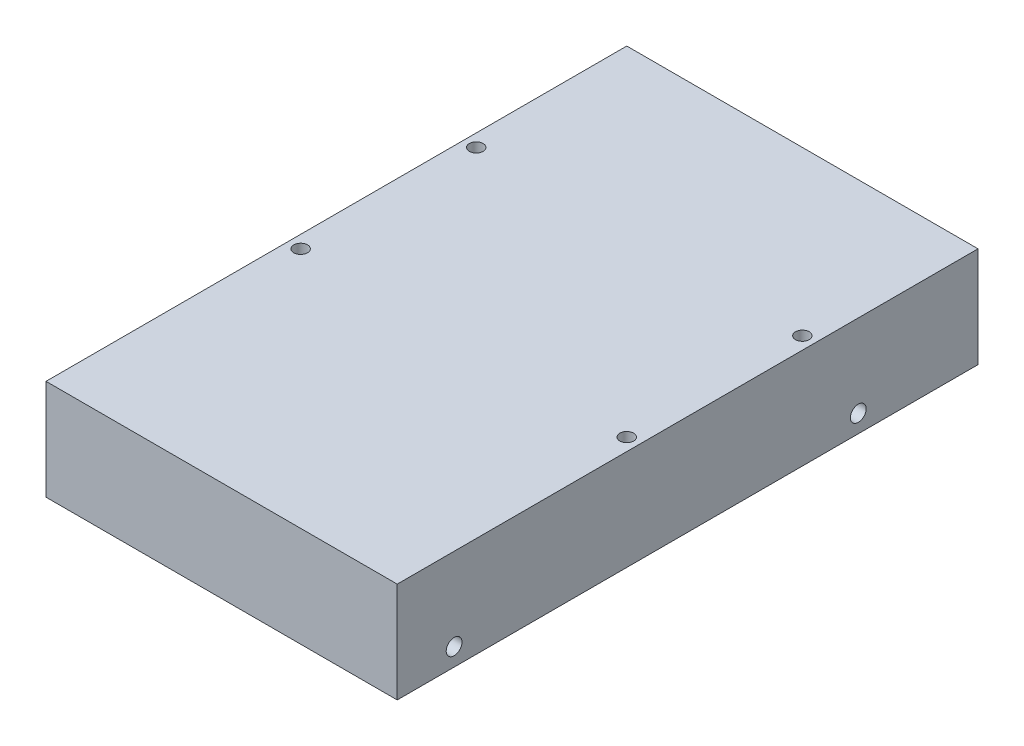
SolidWorks part; units mm, degrees
ref_plane "Front Plane" through (0, 0, 0) normal (0, 0, 1) x (1, 0, 0)
ref_plane "Top Plane" through (0, 0, 0) normal (0, 1, 0) x (1, 0, 0)
ref_plane "Right Plane" through (0, 0, 0) normal (1, 0, 0) x (0, 0, -1)
sketch "Sketch1" plane through (0, 0, 0) normal (0, 1, 0) x (1, 0, 0)
  line L1 (-44.45, -73.5) -> (44.45, -73.5)
  line L2 (-44.45, -73.5) -> (-44.45, 73.5)
  line L3 (-44.45, 73.5) -> (44.45, 73.5)
  line L4 (44.45, -73.5) -> (44.45, 73.5)
  line L5 (-44.45, -73.5) -> (44.45, 73.5) construction
  line L6 (-44.45, 73.5) -> (44.45, -73.5) construction
  point P0 (0, 0)
  dimension "D1" = 147
  dimension "D2" = 88.9
extrude "Boss-Extrude1" add sketch "Sketch1" along normal blind 25.4
sketch "Sketch2" plane through (0, 0, 0) normal (0, -1, 0) x (1, 0, 0)
  line L0 (44.45, 73.5) -> (44.45, -73.5) construction
  line L1 (44.45, -73.5) -> (-44.45, -73.5) construction
  line L2 (41.27, 12.23) -> (41.27, -32.22) construction
  line L3 (-41.27, 12.23) -> (-41.27, -32.22) construction
  line L4 (-44.45, -73.5) -> (-44.45, 73.5) construction
  circle A0 centre (41.27, -32.22) radius 1.7424
  circle A1 centre (41.27, 12.23) radius 1.7424
  circle A2 centre (-41.27, -32.22) radius 1.7424
  circle A3 centre (-41.27, 12.23) radius 1.7424
  dimension "D1" = 3.4849
  dimension "D5" = 3.4849
  dimension "D8" = 3.4849
  dimension "D9" = 3.4849
  dimension "D2" = 3.18
  dimension "D3" = 41.28
  dimension "D4" = 44.45
  dimension "D6" = 41.28
  dimension "D7" = 44.45
  dimension "D10" = 3.18
extrude "Cut-Extrude1" cut sketch "Sketch2" against normal blind 30
sketch "Sketch3" plane through (44.45, 0, 0) normal (1, 0, 0) x (0, 0, -1)
  line L0 (-73.5, 25.4) -> (-73.5, 0) construction
  line L1 (-73.5, 0) -> (73.5, 0) construction
  line L2 (-57.1, 4.5) -> (41.2, 4.5) construction
  circle A0 centre (-59.1, 4.5) radius 2
  circle A1 centre (43.2, 4.5) radius 2
  dimension "D1" = 4
  dimension "D2" = 14.4
  dimension "D3" = 4.5
  dimension "D4" = 98.3
  dimension "D5" = 4
extrude "Cut-Extrude2" cut sketch "Sketch3" against normal up to next
